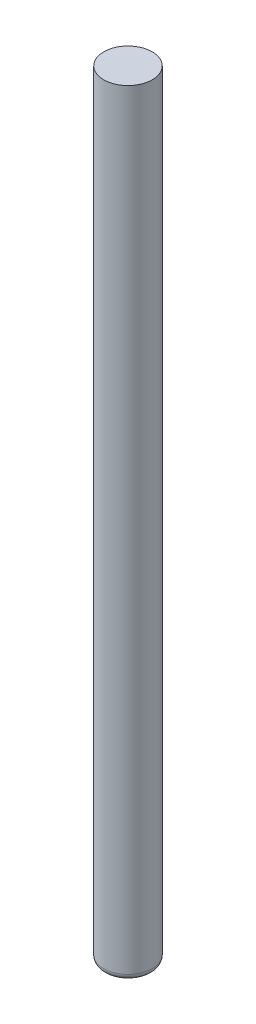
SolidWorks part; units mm, degrees
material "Stainless Steel (ferritic)"
ref_plane "Front Plane" through (0, 0, 0) normal (0, 0, 1) x (1, 0, 0)
ref_plane "Top Plane" through (0, 0, 0) normal (0, 1, 0) x (1, 0, 0)
ref_plane "Right Plane" through (0, 0, 0) normal (1, 0, 0) x (0, 0, -1)
sketch "Sketch1" plane through (0, 0, 0) normal (0, 1, 0) x (1, 0, 0)
  circle A0 centre (0, 0) radius 2
extrude "Boss-Extrude1" add sketch "Sketch1" along normal blind 64
fillet "Fillet1" radius 0.5 1 edges at (0, 0, 2)
